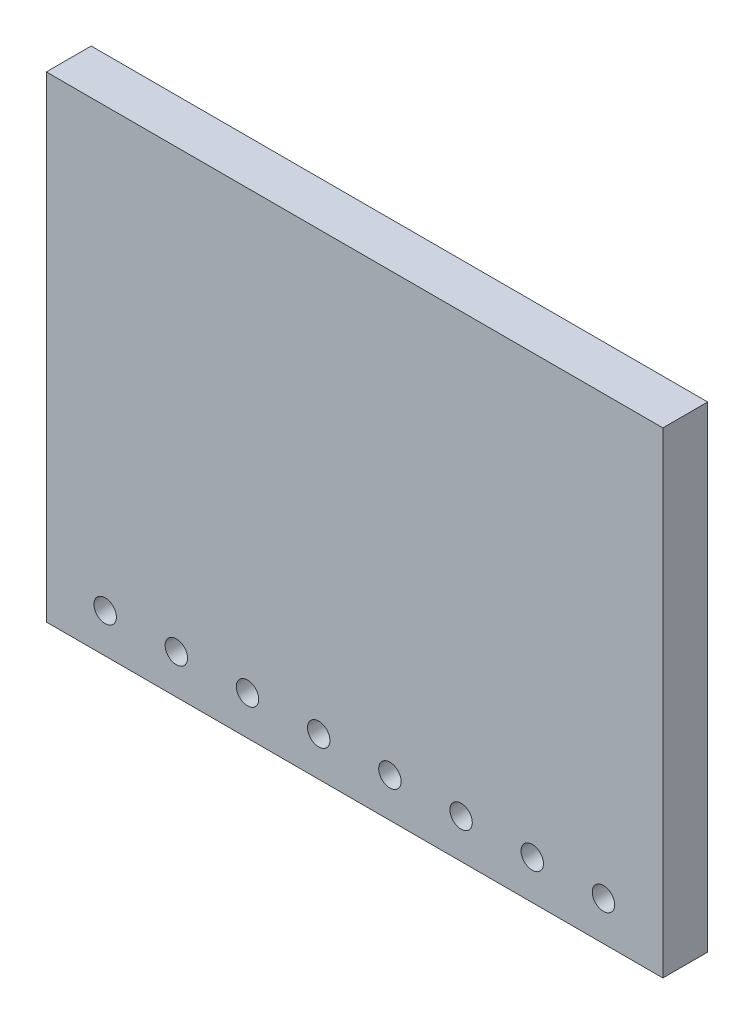
SolidWorks part; units mm, degrees
ref_plane "Front Plane" through (0, 0, 0) normal (0, 0, 1) x (1, 0, 0)
ref_plane "Top Plane" through (0, 0, 0) normal (0, 1, 0) x (1, 0, 0)
ref_plane "Right Plane" through (0, 0, 0) normal (1, 0, 0) x (0, 0, -1)
sketch "Sketch1" plane through (0, 0, 0) normal (0, 0, 1) x (1, 0, 0)
  line L1 (11, 8.5) -> (-11, 8.5)
  line L2 (11, 8.5) -> (11, -8.5)
  line L3 (11, -8.5) -> (-11, -8.5)
  line L4 (-11, 8.5) -> (-11, -8.5)
  line L5 (11, 8.5) -> (-11, -8.5) construction
  line L6 (11, -8.5) -> (-11, 8.5) construction
  point P0 (0, 0)
  dimension "D1" = 22
  dimension "D2" = 17
extrude "Boss-Extrude1" add sketch "Sketch1" along normal blind 1.6
sketch "Sketch2" plane through (0, 0, 1.6) normal (0, 0, 1) x (1, 0, 0)
  line L0 (-11, 8.5) -> (-11, -8.5) construction
  line L2 (-11, -8.5) -> (11, -8.5) construction
  circle A0 centre (-8.9, -7.1) radius 0.4
  circle A1 centre (-6.36, -7.1) radius 0.4
  circle A2 centre (-3.82, -7.1) radius 0.4
  circle A3 centre (-1.28, -7.1) radius 0.4
  circle A4 centre (1.26, -7.1) radius 0.4
  circle A5 centre (3.8, -7.1) radius 0.4
  circle A6 centre (6.34, -7.1) radius 0.4
  circle A7 centre (8.88, -7.1) radius 0.4
  dimension "D1" = 0.8
  dimension "D2" = 2.54
  dimension "D3" = 2.1
  dimension "D4" = 2.54
  dimension "D5" = 2.54
  dimension "D6" = 2.54
  dimension "D7" = 2.54
  dimension "D8" = 2.54
  dimension "D9" = 2.54
  dimension "D10" = 1.4
  dimension "D11" = 1.4
  dimension "D12" = 1.4
  dimension "D13" = 1.4
  dimension "D14" = 1.4
  dimension "D15" = 1.4
  dimension "D16" = 1.4
  dimension "D17" = 1.4
extrude "Cut-Extrude1" cut sketch "Sketch2" against normal up to next
